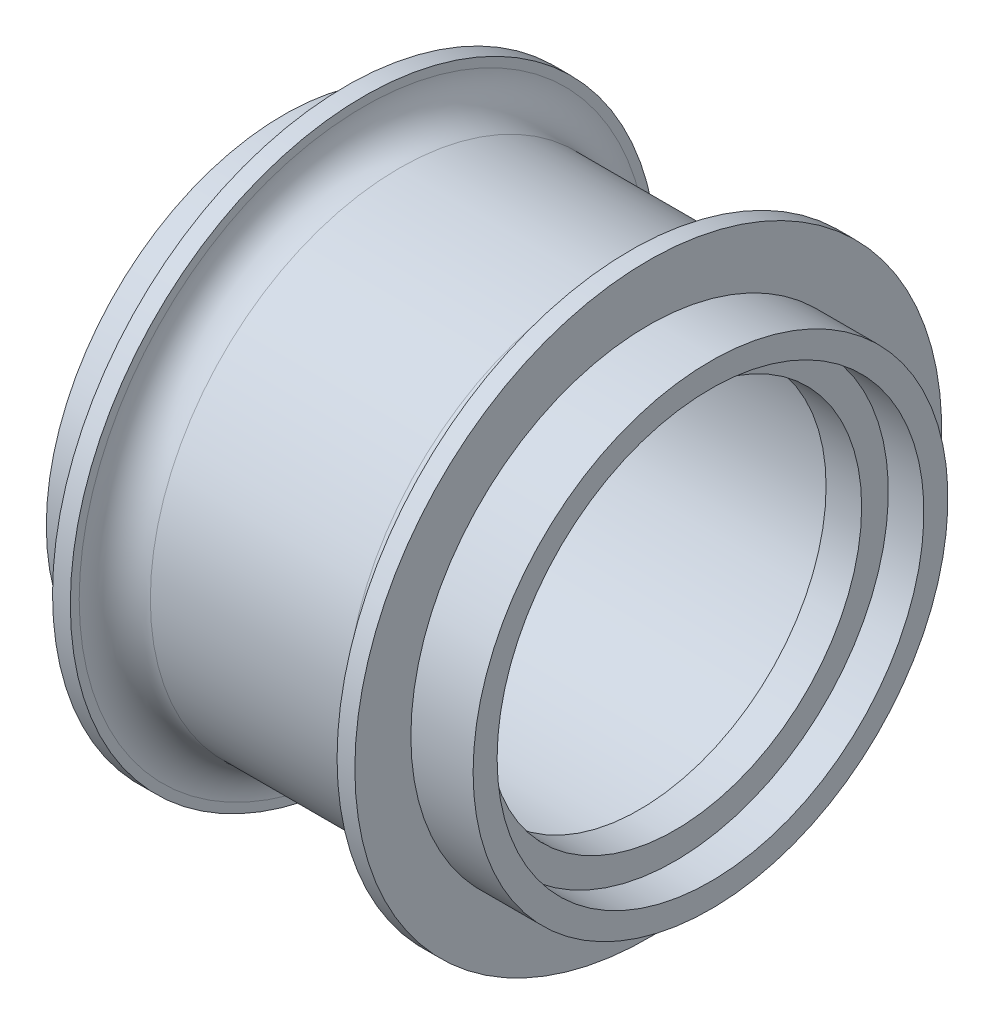
SolidWorks part; units mm, degrees
material "6061-T6 (SS)"
ref_plane "Płaszczyzna XY" through (0, 0, 0) normal (0, 0, 1) x (1, 0, 0)
ref_plane "Płaszczyzna XZ" through (0, 0, 0) normal (0, 1, 0) x (1, 0, 0)
ref_plane "Płaszczyzna YZ" through (0, 0, 0) normal (1, 0, 0) x (0, 0, -1)
sketch "Szkic1" plane through (0, 0, 0) normal (0, 0, 1) x (1, 0, 0)
  line L0 (-7.002, 0) -> (31.0108, 0) construction
  line L1 (-12, 12) -> (-9.3, 12)
  line L2 (-9.3, 12) -> (-9.3, 12.6)
  line L3 (-9.3, 12.6) -> (-8, 12.6)
  line L4 (-8, 12.6) -> (-8, 12)
  line L5 (-8, 12) -> (8, 12)
  line L6 (8, 12) -> (8, 10.5)
  line L7 (8, 10.5) -> (10, 10.5)
  line L9 (12, 13.35) -> (8.5, 13.35)
  line L10 (8.5, 13.35) -> (8.5, 16.5)
  line L11 (8.5, 16.5) -> (7.5, 16.5)
  line L13 (-12, 13.35) -> (-8.5, 13.35)
  line L14 (-8.5, 13.35) -> (-8.5, 16.5)
  line L15 (-8.5, 16.5) -> (-7.5, 16.5)
  line L16 (-7.5, 16.5) -> (-7.5, 16)
  line L17 (-5.5, 14) -> (5.5, 14)
  line L18 (7.5, 16) -> (7.5, 16.5)
  line L19 (10, 10.5) -> (10, 12)
  line L20 (10, 12) -> (12, 12)
  line L21 (0, 0) -> (0, 19.2409) construction
  line L48 (12, 13.35) -> (12, 12)
  line L49 (-12, 13.35) -> (-12, 12)
  arc A0 (5.5, 14) -> (7.5, 16) centre (5.5, 16) ccw
  arc A1 (-7.5, 16) -> (-5.5, 14) centre (-5.5, 16) ccw
  point P33 (0, 12)
  dimension "D11" = 2
  dimension "D2" = 16
  dimension "D3" = 24
  dimension "D4" = 1.3
  dimension "D5" = 28
  dimension "D6" = 3.5
  dimension "D7" = 3.5
  dimension "D8" = 1
  dimension "D9" = 1
  dimension "D10" = 33
  dimension "D12" = 21
  dimension "D13" = 25.2
  dimension "D14" = 24
  dimension "D15" = 26.7
  dimension "D18" = 2
revolve "Obrót1" add sketch "Szkic1" angle 360 about L0
